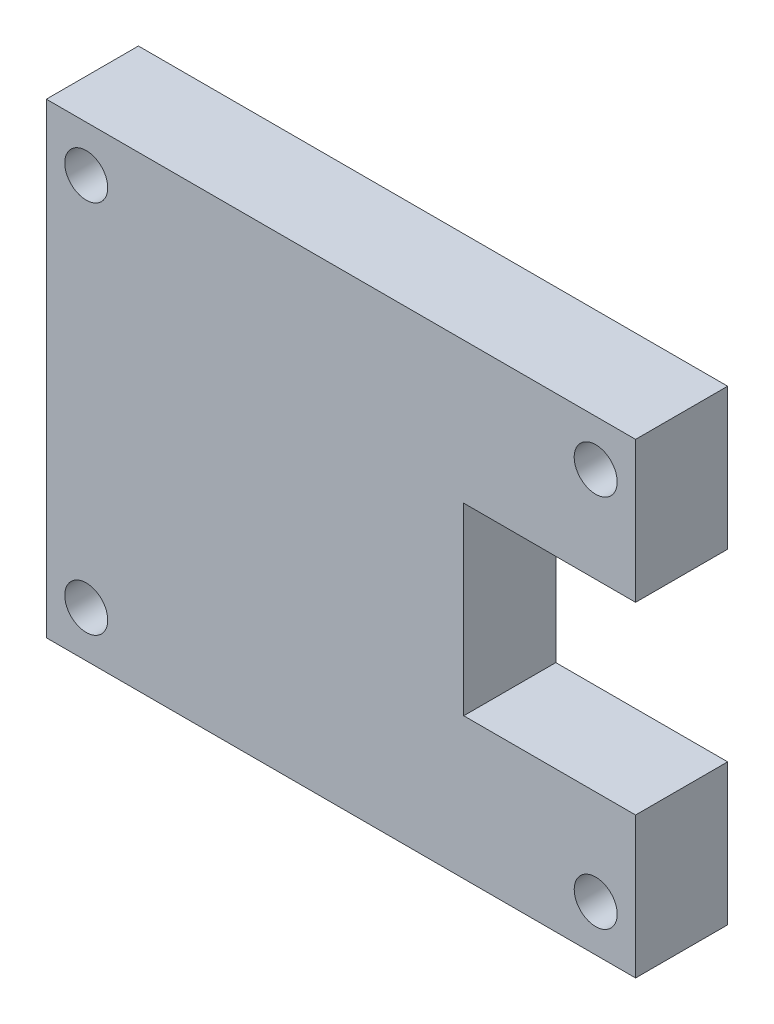
SolidWorks part; units mm, degrees
ref_plane "Plan de face" through (0, 0, 0) normal (0, 0, 1) x (1, 0, 0)
ref_plane "Plan de dessus" through (0, 0, 0) normal (0, 1, 0) x (1, 0, 0)
ref_plane "Plan de droite" through (0, 0, 0) normal (1, 0, 0) x (0, 0, -1)
sketch "Esquisse1" plane through (0, 0, 0) normal (0, 0, 1) x (1, 0, 0)
  line L1 (-24, -19) -> (24, -19)
  line L2 (-24, -19) -> (-24, 19)
  line L3 (-24, 19) -> (24, 19)
  line L4 (24, -19) -> (24, 19)
  line L5 (-24, -19) -> (24, 19) construction
  line L6 (-24, 19) -> (24, -19) construction
  point P0 (0, 0)
  dimension "D1" = 48
  dimension "D2" = 38
extrude "Boss.-Extru.1" add sketch "Esquisse1" along normal blind 7.5
sketch "Esquisse2" plane through (0, 0, 7.5) normal (0, 0, 1) x (1, 0, 0)
  line L0 (24, -19) -> (24, 19) construction
  line L1 (22.5, 15.25) -> (24, 15.25) construction
  line L2 (20.75, 17) -> (20.75, 19) construction
  line L3 (24, 19) -> (-24, 19) construction
  line L4 (0, 19) -> (0, -19) construction
  line L5 (-24, -19) -> (24, -19) construction
  line L6 (-24, 0) -> (24, 0) construction
  line L7 (-24, 19) -> (-24, -19) construction
  circle A0 centre (20.75, 15.25) radius 1.75
  circle A2 centre (-20.75, 15.25) radius 1.75
  circle A3 centre (20.75, -15.25) radius 1.75
  circle A4 centre (-20.75, -15.25) radius 1.75
  dimension "D3" = 41.5
  dimension "D1" = 1.5
  dimension "D2" = 2
extrude "Enlèv. mat.-Extru.1" cut sketch "Esquisse2" against normal blind 7.5
sketch "Esquisse4" plane through (0, 0, 7.5) normal (0, 0, 1) x (1, 0, 0)
  line L0 (24, 7.5) -> (10, 7.5)
  line L1 (24, -19) -> (24, 19) construction
  line L2 (10, 7.5) -> (10, -7.5)
  line L3 (10, -7.5) -> (24, -7.5)
  line L4 (24, 7.5) -> (24, 19)
  line L5 (24, -7.5) -> (24, -19)
  line L6 (24, 7.5) -> (24, -7.5)
  line M10 (24, -19) -> (24, 19)
  dimension "D1" = 15
  dimension "D2" = 14
extrude "Enlèv. mat.-Extru.2" cut sketch "Esquisse4" against normal blind 7.5 contours L2 L3 L0 M10
